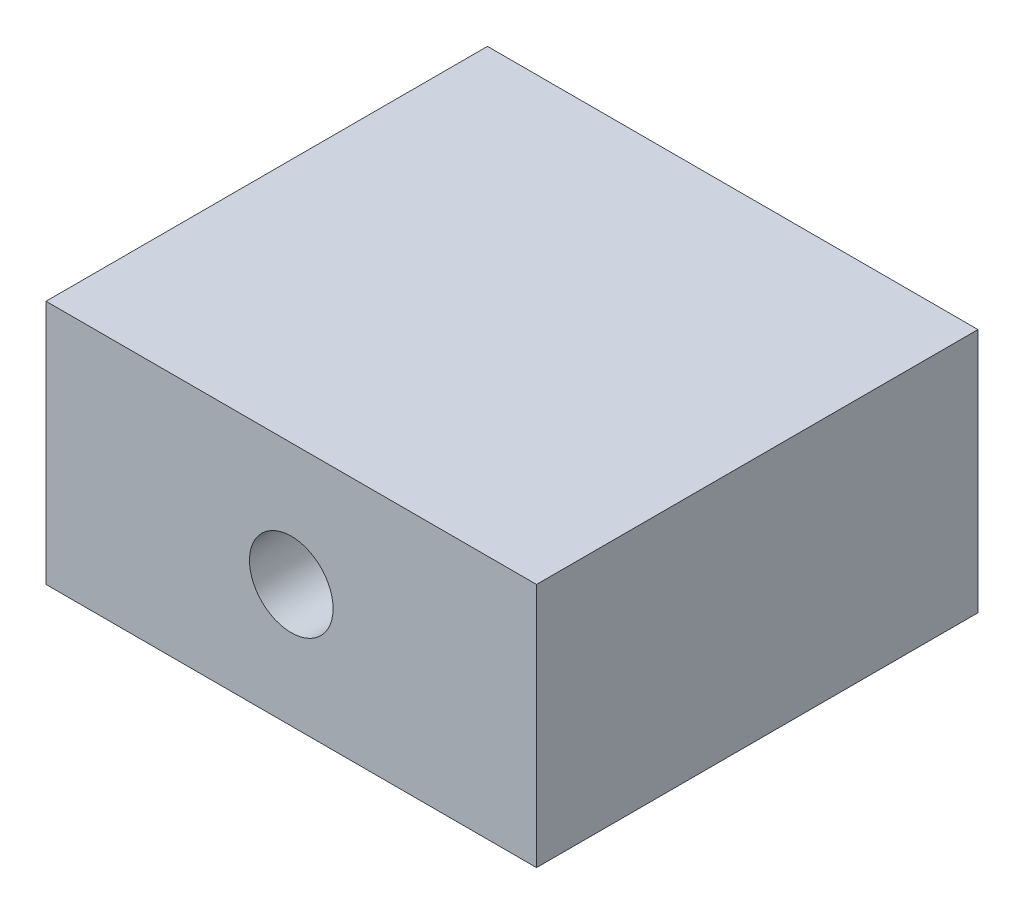
SolidWorks part; units mm, degrees
ref_plane "Front Plane" through (0, 0, 0) normal (0, 0, 1) x (1, 0, 0)
ref_plane "Top Plane" through (0, 0, 0) normal (0, 1, 0) x (1, 0, 0)
ref_plane "Right Plane" through (0, 0, 0) normal (1, 0, 0) x (0, 0, -1)
sketch "Sketch1" plane through (0, 0, 0) normal (0, 1, 0) x (1, 0, 0)
  line L2 (-8, -38) -> (-28, -38)
  line L7 (-8, -20) -> (-8, -38)
  line L8 (-28, -38) -> (-28, -20)
  line L9 (-28, -20) -> (-8, -20)
  dimension "D1" = 20
  dimension "D2" = 18
extrude "Boss-Extrude1" add sketch "Sketch1" along normal blind 10
sketch "Sketch2" plane through (0, 0, 38) normal (0, 0, 1) x (1, 0, 0)
  line L0 (-28, 10) -> (-8, 10) construction
  line L2 (-8, 10) -> (-8, 0) construction
  circle A0 centre (-18, 5) radius 1.705
  dimension "D1" = 3.41
  dimension "D2" = 5
  dimension "D3" = 10
extrude "Cut-Extrude1" cut sketch "Sketch2" against normal blind 15
sketch "Sketch3" plane through (0, 0, 23) normal (0, 0, 1) x (1, 0, 0)
  line L0 (-28, 0) -> (-8, 0) construction
  line L1 (-21.65, 0) -> (-14.35, 0)
  line L2 (-21.65, 0) -> (-21.65, 8.65)
  line L3 (-21.65, 8.65) -> (-14.35, 8.65)
  line L4 (-14.35, 0) -> (-14.35, 8.65)
  circle A0 centre (-18, 5) radius 1.705 construction
  dimension "D2" = 3.65
  dimension "D1" = 3.65
  dimension "D3" = 3.65
extrude "Cut-Extrude2" cut sketch "Sketch3" along normal blind 8
